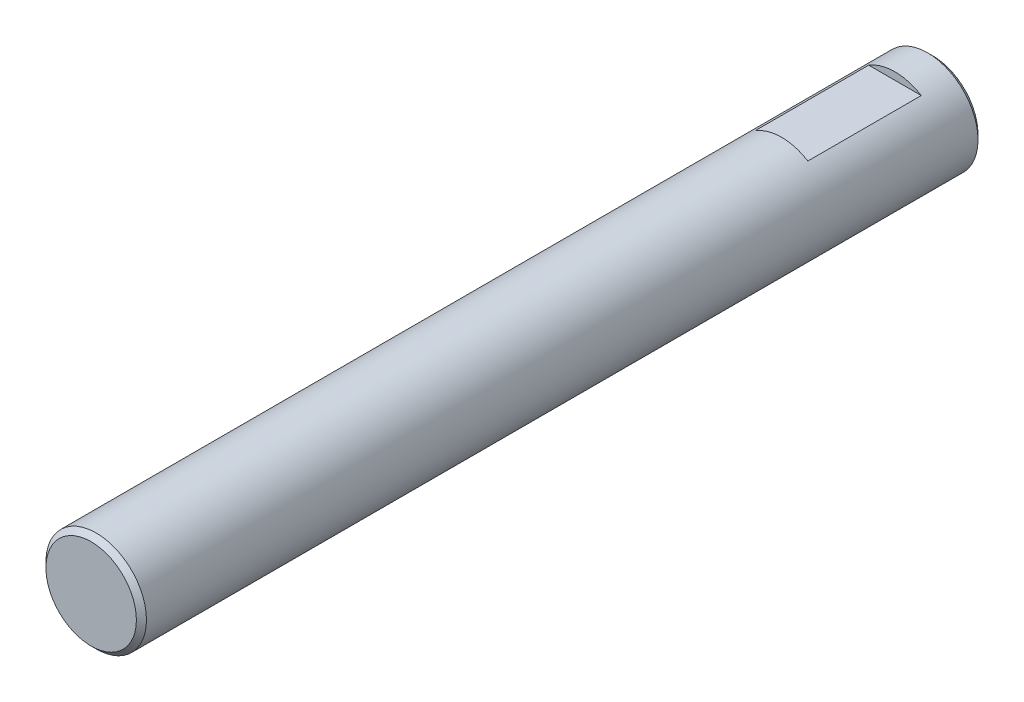
SolidWorks part; units mm, degrees
ref_plane "Front Plane" through (0, 0, 0) normal (0, 0, 1) x (1, 0, 0)
ref_plane "Top Plane" through (0, 0, 0) normal (0, 1, 0) x (1, 0, 0)
ref_plane "Right Plane" through (0, 0, 0) normal (1, 0, 0) x (0, 0, -1)
sketch "Sketch1" plane through (0, 0, 0) normal (0, 0, 1) x (1, 0, 0)
  circle A0 centre (0, 0) radius 1.995
  dimension "D1" = 3.99
extrude "Boss-Extrude1" add sketch "Sketch1" along normal blind 33.4
sketch "Sketch2" plane through (0, 0, 0) normal (1, 0, 0) x (0, 0, -1)
  line L0 (0, -1.995) -> (0, 1.995) construction
  line L1 (-1.5, 2.6204) -> (-6, 2.6204)
  line L2 (-1.5, 2.6204) -> (-1.5, 1.7)
  line L3 (-1.5, 1.7) -> (-6, 1.7)
  line L4 (-6, 2.6204) -> (-6, 1.7)
  line L5 (-7.2858, 0) -> (2.8383, 0) construction
  line L6 (-6, -2.6204) -> (-6, -1.7)
  line L7 (-1.5, -1.7) -> (-6, -1.7)
  line L8 (-1.5, -2.6204) -> (-1.5, -1.7)
  line L9 (-1.5, -2.6204) -> (-6, -2.6204)
  point P6 (-3.75, 1.7)
  dimension "D1" = 3.75
  dimension "D2" = 4.5
  dimension "D3" = 3.4
extrude "Cut-Extrude1" cut sketch "Sketch2" against normal through all both and the other way through all
chamfer "Chamfer1" distance 0.2 angle 45 2 edges at (1.995, 0, 33.4) (1.995, 0, 0)
